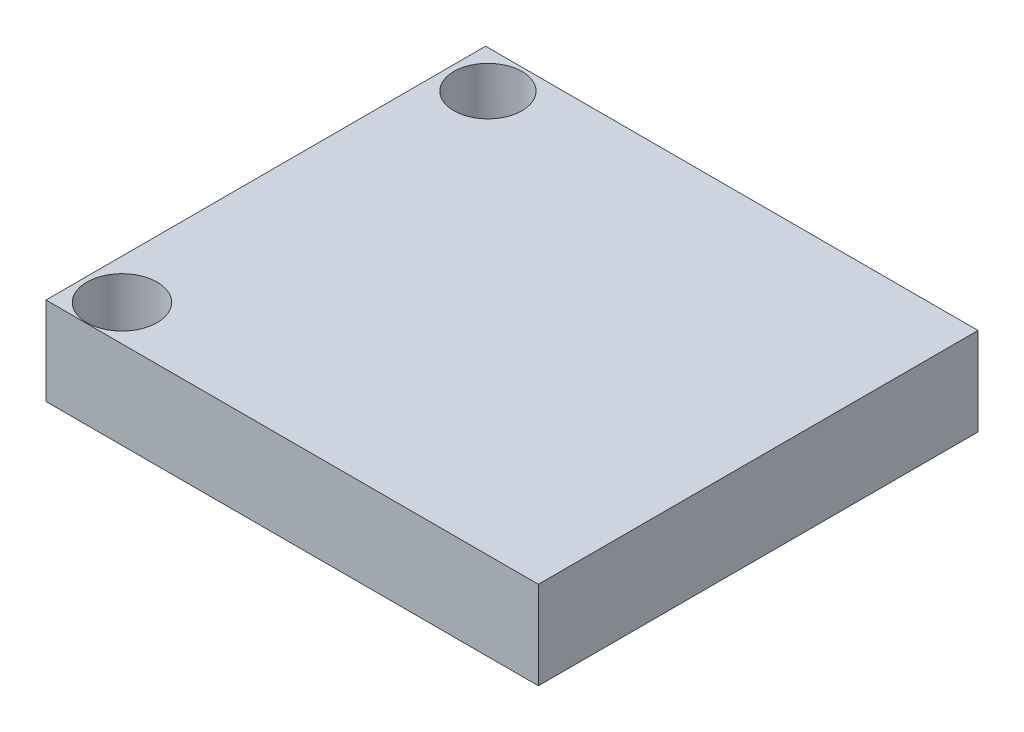
SolidWorks part; units mm, degrees
ref_plane "Płaszczyzna przednia" through (0, 0, 0) normal (0, 0, 1) x (1, 0, 0)
ref_plane "Płaszczyzna górna" through (0, 0, 0) normal (0, 1, 0) x (1, 0, 0)
ref_plane "Płaszczyzna prawa" through (0, 0, 0) normal (1, 0, 0) x (0, 0, -1)
sketch "Sketch1" plane through (0, 0, 0) normal (0, 1, 0) x (1, 0, 0)
  line L1 (-14, -12.5) -> (14, -12.5)
  line L2 (-14, -12.5) -> (-14, 12.5)
  line L3 (-14, 12.5) -> (14, 12.5)
  line L4 (14, -12.5) -> (14, 12.5)
  line L5 (-14, -12.5) -> (14, 12.5) construction
  line L6 (-14, 12.5) -> (14, -12.5) construction
  point P0 (0, 0)
  dimension "D1" = 28
  dimension "D2" = 25
extrude "Boss-Extrude1" add sketch "Sketch1" along normal blind 5
sketch "Sketch2" plane through (0, 5, 0) normal (0, 1, 0) x (1, 0, 0)
  circle A0 centre (-11.7237, 10.3533) radius 1.9369
  circle A1 centre (-11.7237, -10.4564) radius 2
  point P2 (-11.7237, -10.4564)
extrude "Cut-Extrude1" cut sketch "Sketch2" against normal blind 10
